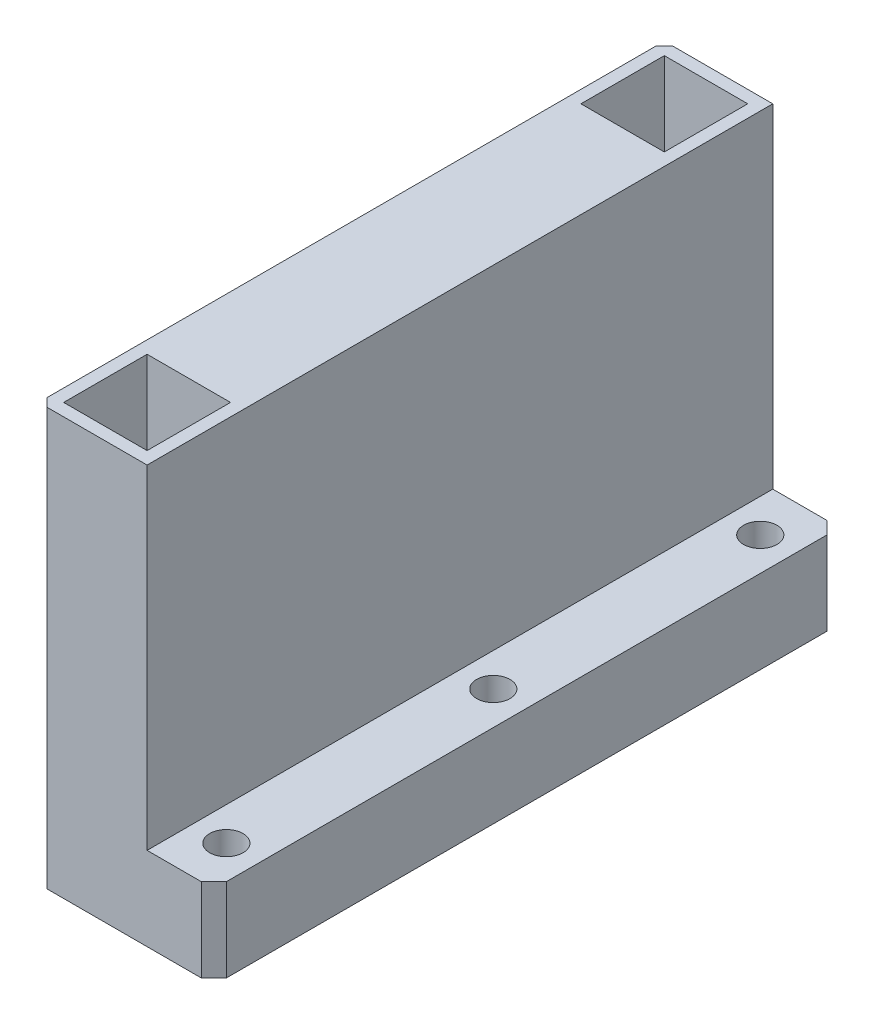
SolidWorks part; units mm, degrees
ref_plane "Front" through (0, 0, 0) normal (0, 0, 1) x (1, 0, 0)
ref_plane "Top" through (0, 0, 0) normal (0, 1, 0) x (1, 0, 0)
ref_plane "Right" through (0, 0, 0) normal (1, 0, 0) x (0, 0, -1)
sketch "Sketch2" plane through (0, 0, 0) normal (0, 0, 1) x (1, 0, 0)
  line L0 (13, 50) -> (13, 10)
  line L1 (0, 0) -> (21, 0)
  line L2 (0, 0) -> (0, 50)
  line L3 (0, 50) -> (13, 50)
  line L4 (21, 0) -> (21, 10)
  line L5 (13, 10) -> (21, 10)
  dimension "D1" = 21
  dimension "D2" = 10
  dimension "D3" = 13
  dimension "D4" = 50
extrude "Boss-Extrude1" add sketch "Sketch2" along normal blind 75
sketch "Sketch3" plane through (0, 50, 0) normal (0, 1, 0) x (1, 0, 0)
  line L0 (1.5, -11.5) -> (11.5, -11.5)
  line L1 (1.5, -1.5) -> (11.5, -1.5)
  line L2 (1.5, -1.5) -> (1.5, -11.5)
  line L3 (1.5, -73.5) -> (11.5, -73.5)
  line L4 (11.5, -1.5) -> (11.5, -11.5)
  line L5 (1.5, -63.5) -> (11.5, -63.5)
  line L6 (1.5, -63.5) -> (1.5, -73.5)
  line L7 (11.5, -63.5) -> (11.5, -73.5)
  line L8 (0, -75) -> (0, 0) construction
  line L9 (13, -75) -> (13, 0) construction
  line L10 (13, 0) -> (0, 0) construction
  line L11 (13, -75) -> (0, -75) construction
  dimension "D1" = 1.5
  dimension "D2" = 1.5
  dimension "D3" = 1.5
  dimension "D4" = 1.5
  dimension "D5" = 10
  dimension "D6" = 10
extrude "Cut-Extrude1" cut sketch "Sketch3" against normal blind 10 contours L4 L1 L2 L0 | L7 L5 L6 L3
sketch "Sketch4" plane through (0, 10, 0) normal (0, 1, 0) x (1, 0, 0)
  line L1 (13, -37.5) -> (19, -37.5) construction
  line L2 (13, -75) -> (13, 0) construction
  line L4 (21, 0) -> (13, 0) construction
  circle A0 centre (17, -5.5) radius 2
  circle A1 centre (17, -37.5) radius 2
  circle A2 centre (17, -69.5) radius 2
  point P14 (17, 0)
  dimension "D2" = 4
  dimension "D1" = 37.5
  dimension "D3" = 32
  dimension "D4" = 32
extrude "Cut-Extrude2" cut sketch "Sketch4" against normal through all contours A2 | L1 A1 | A1 L1 | A0
chamfer "Chamfer1" distance 1.5 angle 45 2 edges at (21, 5, 0) (21, 5, 75)
chamfer "Chamfer2" distance 1 angle 45 2 edges at (0, 25, 0) (0, 25, 75)
